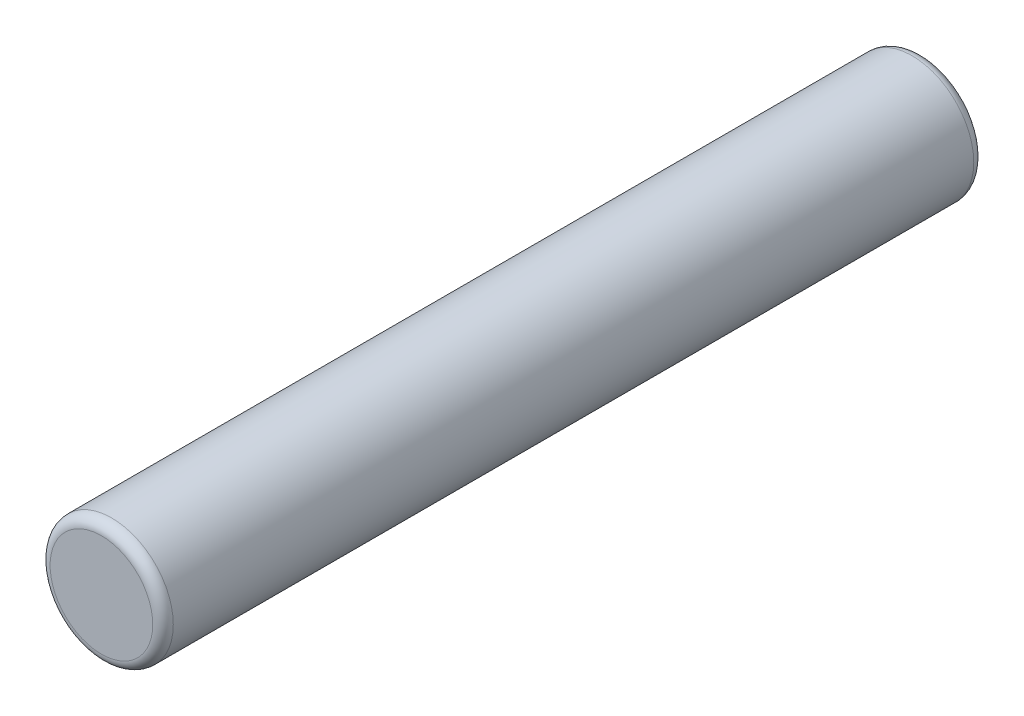
SolidWorks part; units mm, degrees
material "Cast Alloy Steel"
ref_plane "Front Plane" through (0, 0, 0) normal (0, 0, 1) x (1, 0, 0)
ref_plane "Top Plane" through (0, 0, 0) normal (0, 1, 0) x (1, 0, 0)
ref_plane "Right Plane" through (0, 0, 0) normal (1, 0, 0) x (0, 0, -1)
sketch "Sketch1" plane through (0, 0, 0) normal (0, 0, 1) x (1, 0, 0)
  circle A0 centre (0, 0) radius 6
  dimension "D1" = 12
extrude "Boss-Extrude1" add sketch "Sketch1" along normal blind 80
fillet "Fillet1" radius 1 2 edges at (6, 0, 0) (6, 0, 80)
